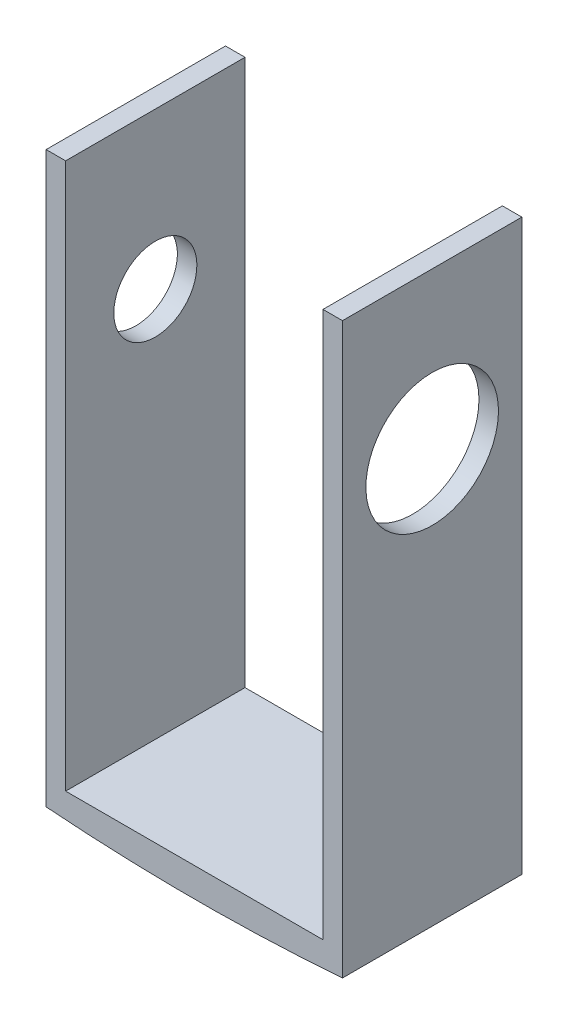
SolidWorks part; units mm, degrees
ref_plane "Front Plane" through (0, 0, 0) normal (0, 0, 1) x (1, 0, 0)
ref_plane "Top Plane" through (0, 0, 0) normal (0, 1, 0) x (1, 0, 0)
ref_plane "Right Plane" through (0, 0, 0) normal (1, 0, 0) x (0, 0, -1)
sketch "Sketch1" plane through (0, 0, 0) normal (0, 0, 1) x (1, 0, 0)
  line L0 (-3.0344, 16.2502) -> (-3.0344, -2.2918)
  line L1 (-3.0344, -2.2918) -> (6.6176, -2.2918)
  line L2 (6.6176, -2.2918) -> (6.6176, 16.2502)
  line L3 (5.9826, 16.2502) -> (5.9826, -1.5298)
  line L4 (5.9826, -1.5298) -> (-2.3994, -1.5298)
  line L5 (-2.3994, -1.5298) -> (-2.3994, 16.2502)
  line L6 (-2.3994, 16.2502) -> (-3.0344, 16.2502)
  line L7 (5.9826, 16.2502) -> (6.6176, 16.2502)
  dimension "D1" = 8.382
  dimension "D2" = 9.652
  dimension "D3" = 0.635
  dimension "D4" = 17.78
  dimension "D5" = 18.542
  dimension "D6" = 17.78
extrude "Boss-Extrude1" add sketch "Sketch1" along normal blind 5.842
sketch "Sketch12" plane through (-3.0344, 0, 0) normal (-1, 0, 0) x (0, 0, 1)
  line L0 (2.921, -2.2918) -> (2.921, 16.2502) construction
  line L1 (5.842, -2.2918) -> (0, -2.2918) construction
  line L2 (5.842, 16.2502) -> (0, 16.2502) construction
sketch "Sketch13" plane through (0, 0, 0) normal (0, 0, 1) x (1, 0, 0)
  line L0 (6.6176, -2.2918) -> (1.7916, 60.2603) construction
  line L1 (1.7916, 60.2603) -> (-3.0344, -2.2918) construction
  dimension "D1" = 62.738
  dimension "D2" = 62.738
sketch "Sketch15" plane through (0, 0, 0) normal (0, 0, 1) x (1, 0, 0)
  line L0 (-3.0344, -2.2918) -> (6.6176, -2.2918) construction
  line L1 (6.6176, -2.2918) -> (-3.0344, -2.2918)
  arc A0 (-3.0344, -2.2918) -> (6.6176, -2.2918) centre (1.7916, 60.2603) ccw
extrude "Boss-Extrude2" add sketch "Sketch15" along normal through all
ref_plane "Plane1" through (0, 0, 2.921) normal (0, 0, 1) x (1, 0, 0)
ref_plane "Plane2" through (1.7916, 0, 0) normal (-1, 0, 0) x (0, 0, 1)
sketch "Sketch18" plane through (5.9826, 0, 0) normal (-1, 0, 0) x (0, 0, 1)
  line L1 (5.842, -1.5298) -> (0, -1.5298) construction
  point P0 (2.921, 11.1702)
  dimension "D1" = 12.7
sketch "Sketch19" plane through (6.6176, 0, 0) normal (1, 0, 0) x (0, 0, -1)
  circle A0 centre (-2.921, 11.1702) radius 2.159
  dimension "D1" = 4.318
extrude "Cut-Extrude1" cut sketch "Sketch19" against normal blind 2.54
hole_wizard "#6-32 Tapped Hole1" positions "Sketch21" profile "Sketch22" tap size "#6-32" standard "ANSI Inch" end condition up to next
sketch "Sketch21" plane through (-3.0344, 0, 0) normal (-1, 0, 0) x (0, 0, 1)
  point P0 (2.921, 11.1702)
sketch "Sketch22" plane through (-3.0344, 11.1702, 2.921) normal (0, 1, 0) x (0, 0, 1)
  line L0 (0, 0) -> (0, 0.635)
  line L1 (0, 0.635) -> (1.3525, 0.635)
  line L2 (1.3525, 0.635) -> (1.3525, 0)
  line L5 (1.3525, 0) -> (0, 0)
  line L11 (0, -6.35) -> (0, 107.95) construction
  dimension "Thread Major Dia." = 2.7051
  dimension "Thru Tap Drill Depth" = 0.635
